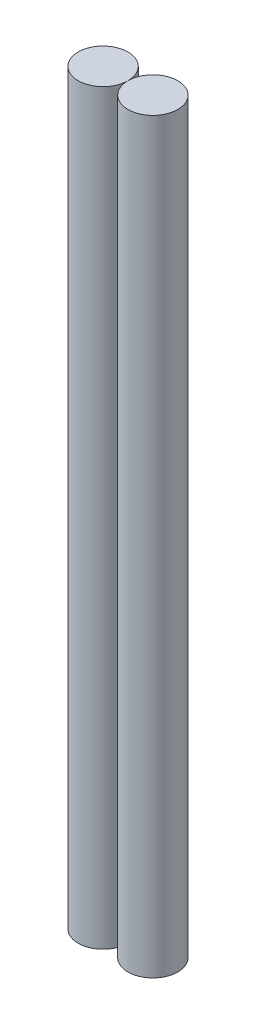
SolidWorks part; units mm, degrees
ref_plane "Front Plane" through (0, 0, 0) normal (0, 0, 1) x (1, 0, 0)
ref_plane "Top Plane" through (0, 0, 0) normal (0, 1, 0) x (1, 0, 0)
ref_plane "Right Plane" through (0, 0, 0) normal (1, 0, 0) x (0, 0, -1)
sketch "Sketch1" plane through (0, 0, 0) normal (0, 1, 0) x (1, 0, 0)
  circle A0 centre (0, 0) radius 9
  circle A1 centre (18, 0) radius 9
  point P5 (0, 0)
  dimension "D1" = 18
extrude "Boss-Extrude1" add sketch "Sketch1" along normal blind 270 contours A0 | A1
